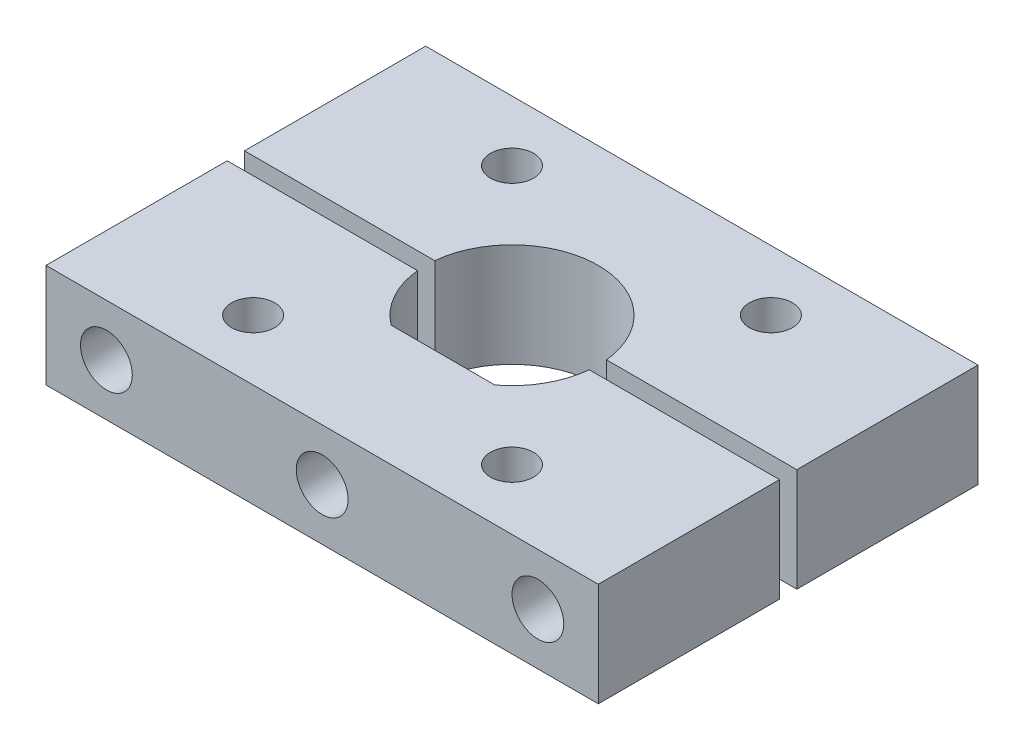
SolidWorks part; units mm, degrees
material "6061 合金"
ref_plane "前视基准面" through (0, 0, 0) normal (0, 0, 1) x (1, 0, 0)
ref_plane "上视基准面" through (0, 0, 0) normal (0, 1, 0) x (1, 0, 0)
ref_plane "右视基准面" through (0, 0, 0) normal (1, 0, 0) x (0, 0, -1)
sketch "草图1" plane through (0, 0, 0) normal (0, 1, 0) x (1, 0, 0)
  line L0 (-3, -4) -> (3, -4)
  line L1 (-16, 11) -> (16, 11)
  line L2 (-16, 11) -> (-16, 0.5)
  line L3 (-16, -11) -> (16, -11)
  line L5 (-4.9749, 0.5) -> (-16, 0.5)
  line L6 (-16, -0.5) -> (-4.9749, -0.5)
  line L7 (-16, -0.5) -> (-16, -11)
  line L8 (-4.9749, 0.5) -> (-4.9749, -0.5) construction
  line L9 (-11, 11) -> (-11, -11) construction
  line L10 (-14, -11) -> (-14, 11) construction
  line L11 (-7.5, 7.5) -> (7.5, -7.5) construction
  line L12 (-7.5, 7.5) -> (7.5, 7.5) construction
  line L13 (-7.5, 7.5) -> (-7.5, -7.5) construction
  line L14 (-7.5, -7.5) -> (7.5, -7.5) construction
  line L15 (7.5, 7.5) -> (7.5, -7.5) construction
  line L16 (0, -55) -> (0, 55) construction
  line L17 (16, -0.5) -> (16, -11)
  line L18 (16, -0.5) -> (4.9749, -0.5)
  line L19 (4.9749, 0.5) -> (16, 0.5)
  line L20 (16, 11) -> (16, 0.5)
  arc A0 (4.9749, 0.5) -> (-4.9749, 0.5) centre (0, 0) ccw
  arc A1 (-4.9749, -0.5) -> (-3, -4) centre (0, 0) ccw
  circle A2 centre (-7.5, 7.5) radius 1.5 construction
  arc A3 (4.9749, -0.5) -> (3, -4) centre (0, 0) cw
  dimension "D1" = 10
  dimension "D6" = 3
  dimension "D9" = 22
  dimension "D2" = 4
  dimension "D3" = 1
  dimension "D4" = 3
  dimension "D5" = 15
  dimension "D7" = 2
  dimension "D8" = 32
extrude "凸台-拉伸1" add sketch "草图1" along normal mid plane 6
hole_wizard "M3 螺纹孔1" positions "草图2" profile "草图3" tap size "M3" standard "GB" end condition through all
sketch "草图2" plane through (0, 0, 11) normal (0, 0, 1) x (1, 0, 0)
  line L0 (-11, 0) -> (-14, 0) construction
  line L3 (0, -55) -> (0, 55) construction
  point P0 (-12.5, 0)
  point P16 (12.5, 0)
sketch "草图3" plane through (-12.5, 0, 11) normal (1, 0, 0) x (0, -1, 0)
  line L0 (0, 0) -> (0, 22)
  line L1 (0, 22) -> (1.25, 22)
  line L2 (1.25, 22) -> (1.25, 0)
  line L5 (1.25, 0) -> (0, 0)
  line L11 (0, -6.35) -> (0, 107.95) construction
  dimension "通孔螺纹孔钻头直径" = 2.5
  dimension "通孔螺纹孔钻头深度" = 22
cosmetic thread "孔螺蚊线7"
cosmetic thread "孔螺蚊线8"
hole_wizard "M3 螺纹孔2" positions "草图4" profile "草图5" tap size "M3" standard "GB" end condition through all
sketch "草图4" plane through (0, 3, 0) normal (0, 1, 0) x (1, 0, 0)
  point P0 (-7.5, 7.5)
  point P3 (7.5, 7.5)
  point P6 (-7.5, -7.5)
  point P9 (7.5, -7.5)
sketch "草图5" plane through (-7.5, 3, -7.5) normal (1, 0, 0) x (0, 0, 1)
  line L0 (0, 0) -> (0, 6)
  line L1 (0, 6) -> (1.25, 6)
  line L2 (1.25, 6) -> (1.25, 0)
  line L5 (1.25, 0) -> (0, 0)
  line L11 (0, -6.35) -> (0, 107.95) construction
  dimension "通孔螺纹孔钻头直径" = 2.5
  dimension "通孔螺纹孔钻头深度" = 6
cosmetic thread "孔螺蚊线3"
cosmetic thread "孔螺蚊线4"
cosmetic thread "孔螺蚊线5"
cosmetic thread "孔螺蚊线6"
sketch "草图6" plane through (0, 0, 11) normal (0, 0, 1) x (1, 0, 0)
  circle A0 centre (0, 0) radius 1.5
  circle A1 centre (-12.5, 0) radius 1.5
  circle A2 centre (12.5, 0) radius 1.5
  dimension "D1" = 3
extrude "切除-拉伸1" cut sketch "草图6" against normal through all
